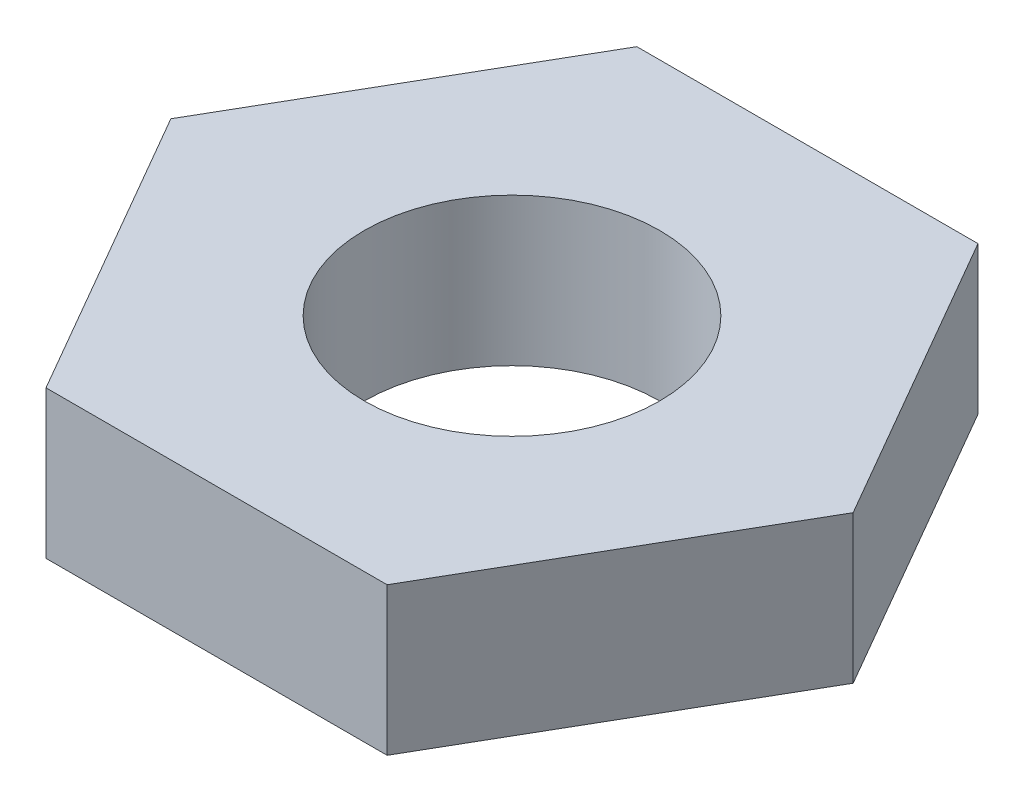
SolidWorks part; units mm, degrees
ref_plane "Спереди" through (0, 0, 0) normal (0, 0, 1) x (1, 0, 0)
ref_plane "Сверху" through (0, 0, 0) normal (0, 1, 0) x (1, 0, 0)
ref_plane "Справа" through (0, 0, 0) normal (1, 0, 0) x (0, 0, -1)
sketch "Эскиз1" plane through (0, 0, 0) normal (0, 1, 0) x (1, 0, 0)
  line L1 (-5.7735, 0) -> (-2.8868, -5)
  line L2 (-2.8868, -5) -> (2.8868, -5)
  line L3 (2.8868, -5) -> (5.7735, 0)
  line L4 (5.7735, 0) -> (2.8868, 5)
  line L5 (2.8868, 5) -> (-2.8868, 5)
  line L6 (-2.8868, 5) -> (-5.7735, 0)
  circle A0 centre (0, 0) radius 5 construction
  circle A1 centre (0, 0) radius 2.5
  dimension "D1" = 5
  dimension "D2" = 10
extrude "Бобышка-Вытянуть1" add sketch "Эскиз1" along normal blind 2.5
